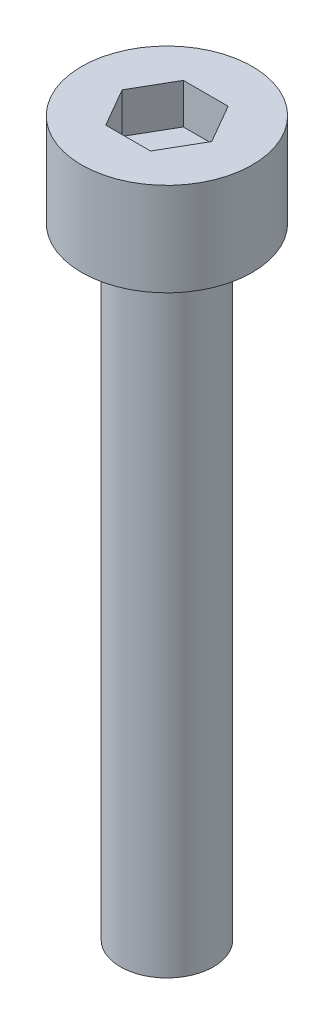
SolidWorks part; units mm, degrees
material "AISI 304"
ref_plane "前视基准面" through (0, 0, 0) normal (0, 0, 1) x (1, 0, 0)
ref_plane "上视基准面" through (0, 0, 0) normal (0, 1, 0) x (1, 0, 0)
ref_plane "右视基准面" through (0, 0, 0) normal (1, 0, 0) x (0, 0, -1)
sketch "草图1" plane through (0, 0, 0) normal (0, 1, 0) x (1, 0, 0)
  circle A0 centre (0, 0) radius 2.75
  dimension "D1" = 5.5
extrude "杯头" add sketch "草图1" along normal blind 3
sketch "草图2" plane through (0, 3, 0) normal (0, 1, 0) x (1, 0, 0)
  line L1 (1.4434, 0) -> (0.7217, 1.25)
  line L2 (0.7217, 1.25) -> (-0.7217, 1.25)
  line L3 (-0.7217, 1.25) -> (-1.4434, 0)
  line L4 (-1.4434, 0) -> (-0.7217, -1.25)
  line L5 (-0.7217, -1.25) -> (0.7217, -1.25)
  line L6 (0.7217, -1.25) -> (1.4434, 0)
  circle A0 centre (0, 0) radius 1.25 construction
  dimension "D1" = 2.5
extrude "内六角口" cut sketch "草图2" against normal blind 1.3
sketch "草图3" plane through (0, 0, 0) normal (0, -1, 0) x (1, 0, 0)
  circle A0 centre (0, 0) radius 1.5
  dimension "D1" = 3
extrude "螺纹长" add sketch "草图3" along normal blind 20
